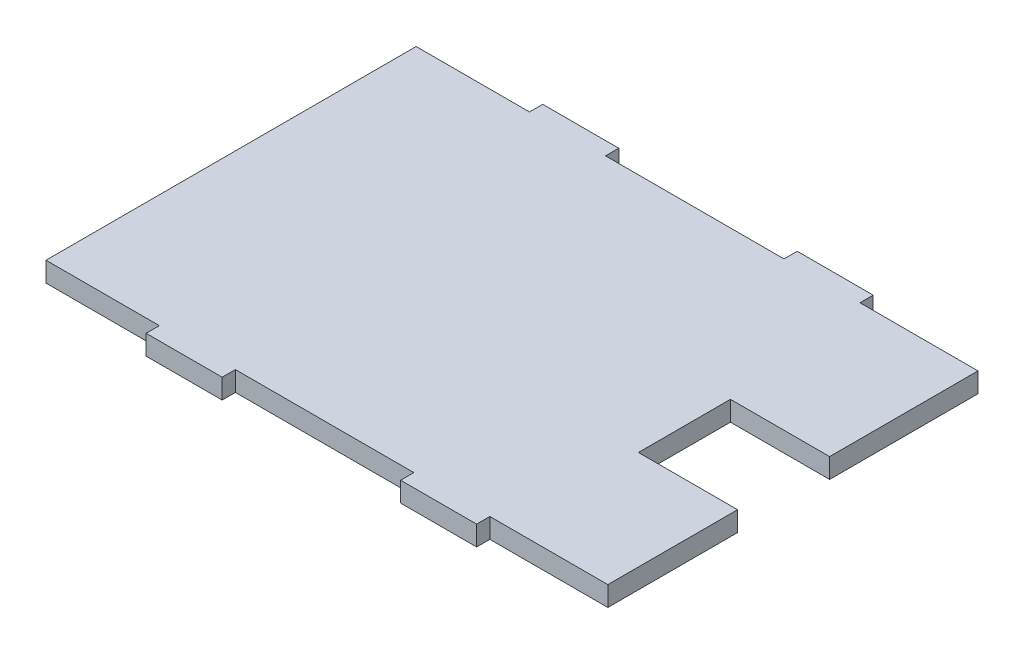
SolidWorks part; units mm, degrees
material "Custom Plastic"
ref_plane "Front Plane" through (0, 0, 0) normal (0, 0, 1) x (1, 0, 0)
ref_plane "Top Plane" through (0, 0, 0) normal (0, 1, 0) x (1, 0, 0)
ref_plane "Right Plane" through (0, 0, 0) normal (1, 0, 0) x (0, 0, -1)
sketch "Sketch1" plane through (0, 0, 0) normal (0, 1, 0) x (1, 0, 0)
  line L0 (-43.18, 0) -> (43.18, 0) construction
  line L1 (-25.7556, -30.48) -> (-14.0716, -30.48)
  line L2 (-43.18, -28.448) -> (-43.18, 28.448) construction
  line L3 (-25.7556, 30.48) -> (-14.0716, 30.48)
  line L4 (43.18, -28.448) -> (43.18, 28.448) construction
  line L5 (13.3604, -30.48) -> (25.0444, -30.48)
  line L6 (25.0444, -28.448) -> (43.18, -28.448)
  line L7 (-43.18, 28.448) -> (-25.7556, 28.448)
  line L8 (-25.7556, 28.448) -> (-25.7556, 30.48)
  line L9 (-14.0716, 30.48) -> (-14.0716, 28.448)
  line L10 (-14.0716, 28.448) -> (13.3604, 28.448)
  line L11 (13.3604, 28.448) -> (13.3604, 30.48)
  line L12 (25.0444, 30.48) -> (25.0444, 28.448)
  line L13 (25.0444, 28.448) -> (43.18, 28.448)
  line L14 (13.3604, 30.48) -> (25.0444, 30.48)
  line L15 (-43.18, 28.448) -> (-43.18, -28.448)
  line L16 (43.18, 28.448) -> (43.18, -28.448)
  line L17 (25.0444, -30.48) -> (25.0444, -28.448)
  line L18 (13.3604, -28.448) -> (13.3604, -30.48)
  line L19 (-14.0716, -28.448) -> (13.3604, -28.448)
  line L20 (-14.0716, -30.48) -> (-14.0716, -28.448)
  line L21 (-25.7556, -28.448) -> (-25.7556, -30.48)
  line L22 (-43.18, -28.448) -> (-25.7556, -28.448)
  line L23 (-25.7556, -30.48) -> (-14.0716, -30.48)
  line L24 (13.3604, -30.48) -> (25.0444, -30.48)
  line L25 (43.18, -8.509) -> (27.94, -8.509)
  line L26 (27.94, -8.509) -> (27.94, 5.6388)
  line L27 (27.94, 5.6388) -> (43.18, 5.6388)
  point P0 (0, 0)
  dimension "D1" = 60.96
  dimension "D2" = 86.36
  dimension "D3" = 2.032
  dimension "D4" = 17.4244
  dimension "D5" = 11.684
  dimension "D6" = 27.432
  dimension "D7" = 43.18
  dimension "D8" = 19.939
  dimension "D9" = 15.24
  dimension "D10" = 14.1478
extrude "Boss-Extrude1" add sketch "Sketch1" along normal blind 3.048 contours L26 L27 L16 L13 L12 L14 L11 L10 L9 L3 L8 L7 L15 L22 L21 L1 L20 L19 L18 L5 L17 L6 L25
